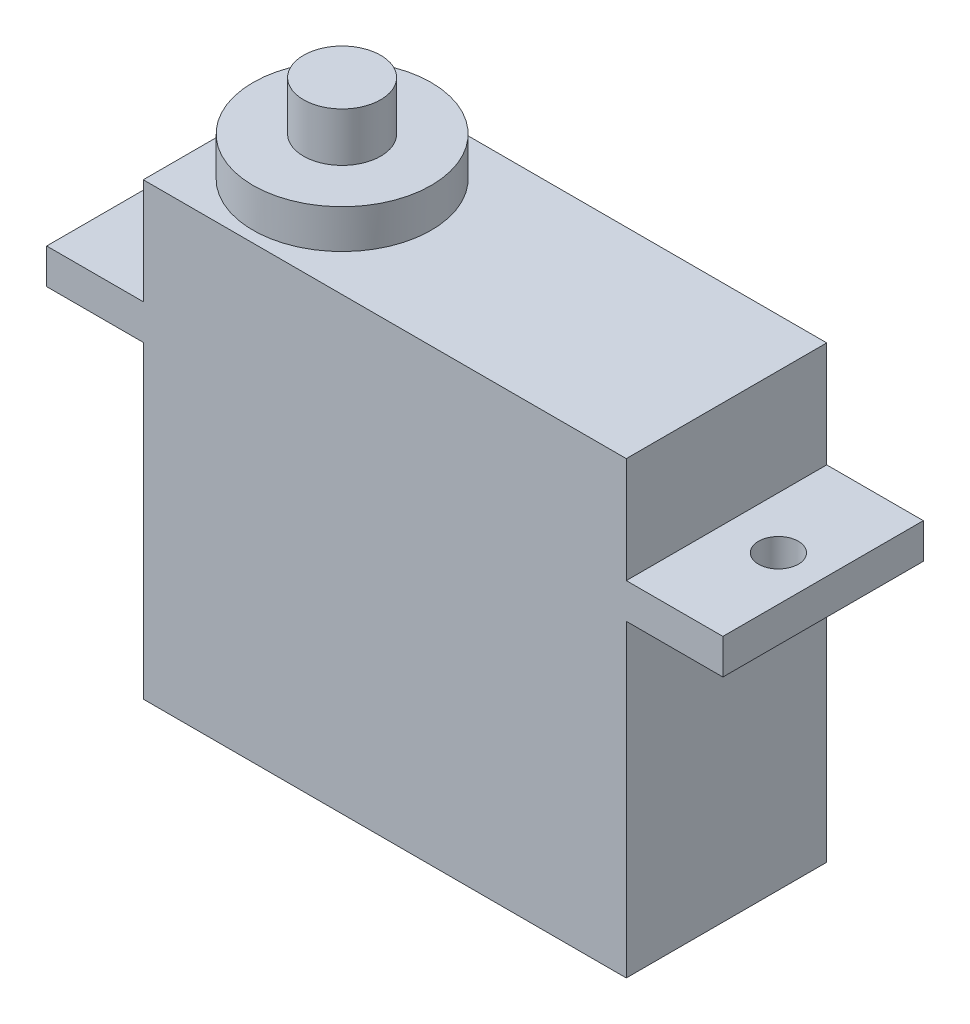
SolidWorks part; units mm, degrees
ref_plane "Front Plane" through (0, 0, 0) normal (0, 0, 1) x (1, 0, 0)
ref_plane "Top Plane" through (0, 0, 0) normal (0, 1, 0) x (1, 0, 0)
ref_plane "Right Plane" through (0, 0, 0) normal (1, 0, 0) x (0, 0, -1)
sketch "Sketch1" plane through (0, 0, 0) normal (0, 0, 1) x (1, 0, 0)
  line L0 (19.1, 1.75) -> (23.9, 1.75)
  line L1 (-4.9, 7) -> (19.1, 7)
  line L2 (-4.9, 7) -> (-4.9, 1.75)
  line L3 (-4.9, -15.35) -> (19.1, -15.35)
  line L4 (19.1, 7) -> (19.1, 1.75)
  line L5 (-9.7, 1.75) -> (-4.9, 1.75)
  line L6 (-9.7, 1.75) -> (-9.7, 0)
  line L7 (-9.7, 0) -> (-4.9, 0)
  line L8 (23.9, 1.75) -> (23.9, 0)
  line L9 (19.1, 0) -> (23.9, 0)
  line L10 (-4.9, 0) -> (-4.9, -15.35)
  line L11 (19.1, 0) -> (19.1, -15.35)
  line L12 (0, 7) -> (0, -15.35) construction
  dimension "D1" = 24
  dimension "D2" = 33.6
  dimension "D3" = 7
  dimension "D4" = 15.35
  dimension "D5" = 4.9
  dimension "D6" = 1.75
extrude "Boss-Extrude1" add sketch "Sketch1" along normal mid plane 9.96
sketch "Sketch2" plane through (0, 1.75, 0) normal (0, 1, 0) x (1, 0, 0)
  line L0 (-7.48, 0) -> (-4.9, 0) construction
  line L1 (-4.9, -4.98) -> (-4.9, 4.98) construction
  line L2 (21.68, 0) -> (19.1, 0) construction
  line L3 (19.1, -4.98) -> (19.1, 4.98) construction
  circle A0 centre (-7.48, 0) radius 0.99
  circle A1 centre (21.68, 0) radius 0.99
  dimension "D3" = 1.98
  dimension "D1" = 7.48
extrude "Cut-Extrude1" cut sketch "Sketch2" against normal through all
sketch "Sketch3" plane through (0, 7, 0) normal (0, 1, 0) x (1, 0, 0)
  circle A0 centre (0, 0) radius 4.4294
extrude "Boss-Extrude2" add sketch "Sketch3" along normal blind 1.93
sketch "Sketch4" plane through (0, 8.93, 0) normal (0, 1, 0) x (1, 0, 0)
  circle A0 centre (0, 0) radius 1.9164
extrude "Boss-Extrude3" add sketch "Sketch4" along normal blind 2.43
